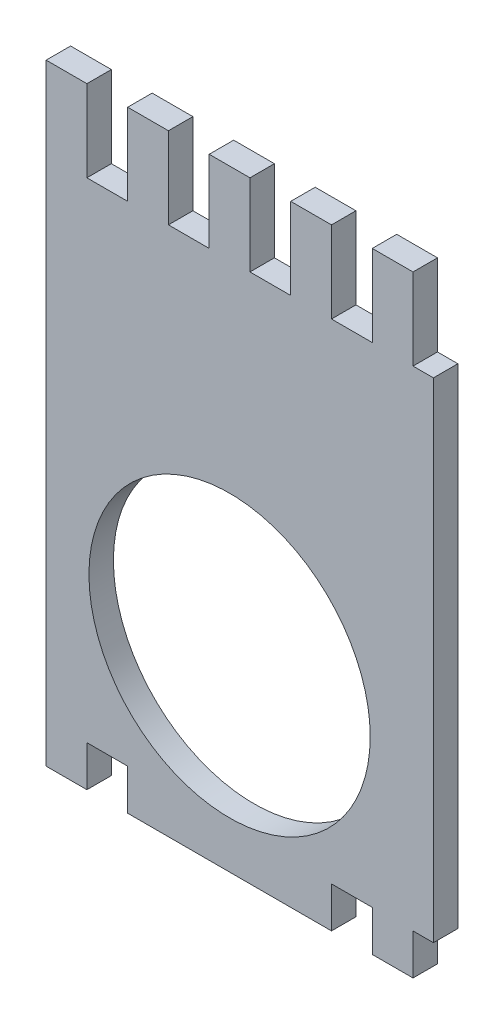
SolidWorks part; units mm, degrees
material "Balsa"
ref_plane "Plan de face" through (0, 0, 0) normal (0, 0, 1) x (1, 0, 0)
ref_plane "Plan de dessus" through (0, 0, 0) normal (0, 1, 0) x (1, 0, 0)
ref_plane "Plan de droite" through (0, 0, 0) normal (1, 0, 0) x (0, 0, -1)
sketch "Esquisse3" plane through (0, 0, 0) normal (0, 0, 1) x (1, 0, 0)
  line L0 (0, 70.5597) -> (0, -65.6935) construction
  line L2 (-25, 20) -> (25, 20)
  line L3 (-25, 20) -> (-25, -40)
  line L4 (-25, -40) -> (25, -40)
  line L5 (25, 20) -> (25, -40)
  dimension "D1" = 20
  dimension "D2" = 25
  dimension "D3" = 50
  dimension "D4" = 60
extrude "Boss.-Extru.12" add sketch "Esquisse3" along normal blind 3
sketch "Esquisse4" plane through (0, 0, 3) normal (0, 0, 1) x (1, 0, 0)
  line L1 (-25, 20) -> (-25, -40) construction
  line L2 (-25, -40) -> (25, -40) construction
  circle A0 centre (0, -22) radius 17.25
  dimension "D1" = 34.5
  dimension "D2" = 25
  dimension "D3" = 18
extrude "Enlèv. mat.-Extru.1" cut sketch "Esquisse4" against normal blind 5
sketch "Esquisse5" plane through (0, 0, 3) normal (0, 0, 1) x (1, 0, 0)
  line L0 (25, 20) -> (-25, 20) construction
  line L1 (-22.5, 30) -> (-17.5, 30)
  line L2 (-22.5, 30) -> (-22.5, 20)
  line L3 (-22.5, 20) -> (-17.5, 20)
  line L4 (-17.5, 30) -> (-17.5, 20)
  line L5 (-25, -40) -> (25, -40) construction
  line L6 (-22.5, -40) -> (-17.5, -40)
  line L7 (-22.5, -40) -> (-22.5, -45)
  line L8 (-22.5, -45) -> (-17.5, -45)
  line L9 (-17.5, -40) -> (-17.5, -45)
  line L10 (-25, 20) -> (-25, -40) construction
  dimension "D1" = 10
  dimension "D2" = 5
  dimension "D3" = 2.5
  dimension "D4" = 5
  dimension "D5" = 5
  dimension "D6" = 2.5
extrude "Boss.-Extru.13" add sketch "Esquisse5" against normal blind 3
pattern_linear "Répétition linéaire1" count 5 spacing 10 along (1, 0, 0) of "Boss.-Extru.13"
sketch "Esquisse6" plane through (0, 0, 3) normal (0, 0, 1) x (1, 0, 0)
  line L1 (-7.5, -40) -> (-2.5, -40)
  line L2 (-7.5, -40) -> (-7.5, -45)
  line L3 (-7.5, -45) -> (-2.5, -45)
  line L4 (-2.5, -40) -> (-2.5, -45)
  line L5 (2.5, -40) -> (7.5, -40)
  line L6 (2.5, -40) -> (2.5, -45)
  line L7 (2.5, -45) -> (7.5, -45)
  line L8 (7.5, -40) -> (7.5, -45)
extrude "Boss.-Extru.14" add sketch "Esquisse6" against normal blind 3
sketch "Esquisse7" plane through (0, 0, 3) normal (0, 0, 1) x (1, 0, 0)
  line L1 (-25, -40) -> (-22.5, -40)
  line L2 (-25, -40) -> (-25, 20)
  line L3 (-25, 20) -> (-22.5, 20)
  line L4 (-22.5, -40) -> (-22.5, 20)
extrude "Enlèv. mat.-Extru.2" cut sketch "Esquisse7" against normal blind 10
